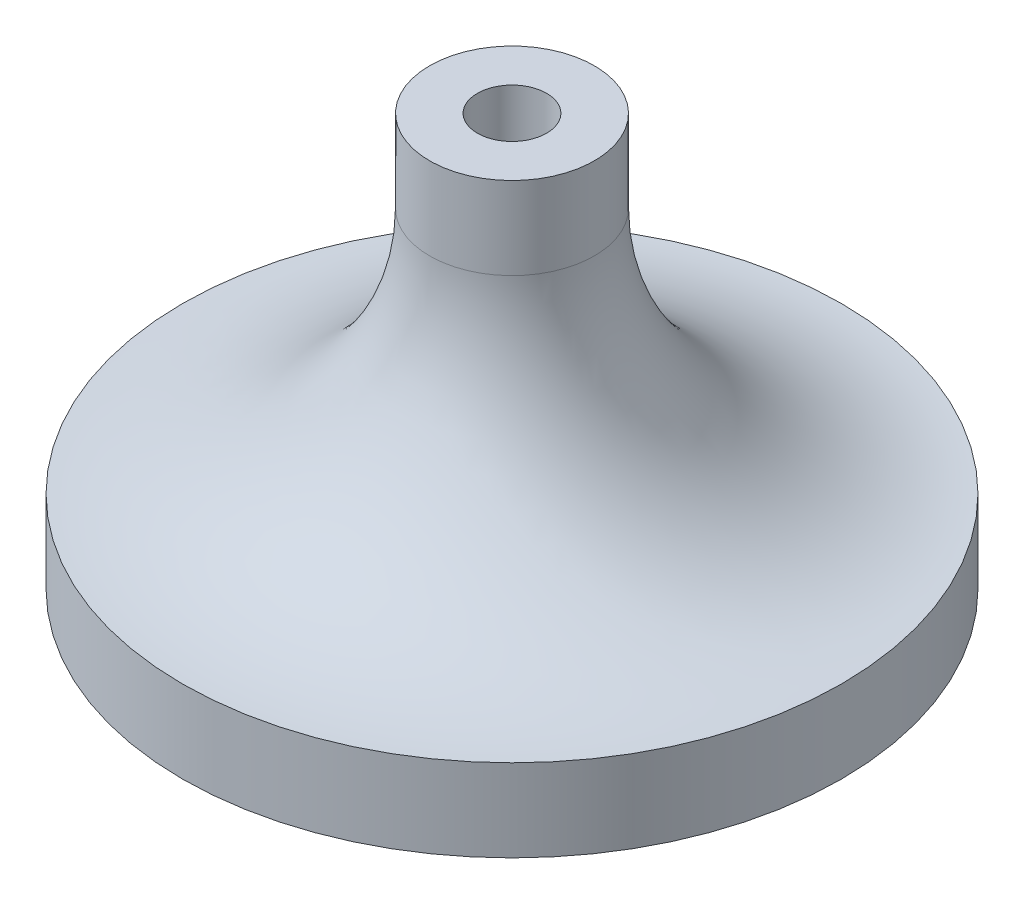
SolidWorks part; units mm, degrees
ref_plane "Front Plane" through (0, 0, 0) normal (0, 0, 1) x (1, 0, 0)
ref_plane "Top Plane" through (0, 0, 0) normal (0, 1, 0) x (1, 0, 0)
ref_plane "Right Plane" through (0, 0, 0) normal (1, 0, 0) x (0, 0, -1)
sketch "Sketch2" plane through (0, 0, 0) normal (0, 0, 1) x (1, 0, 0)
  line L0 (0, 0) -> (-20, 0)
  line L1 (-20, 0) -> (-20, 5)
  line L2 (-5, 20) -> (-5, 25)
  line L3 (-5, 25) -> (0, 25)
  line L4 (0, 25) -> (0, 0)
  arc A0 (-20, 5) -> (-5, 20) centre (-20, 20) ccw
  dimension "D1" = 20
  dimension "D2" = 5
  dimension "D3" = 5
  dimension "D4" = 25
revolve "Revolve1" add sketch "Sketch2" angle 360 about L4
hole_wizard "M5x0.8 Tapped Hole1" positions "Sketch3" profile "Sketch5" tap size "M5x0.8" standard "ANSI Metric"
sketch "Sketch3" plane through (0, 25, 0) normal (0, 1, 0) x (1, 0, 0)
  point P0 (0, 0)
sketch "Sketch5" plane through (0, 25, 0) normal (1, 0, 0) x (0, 0, 1)
  line L0 (0, 0) -> (0, 20.2618)
  line L1 (0, 20.2618) -> (2.1, 19)
  line L2 (2.1, 19) -> (2.1, 0)
  line L5 (2.1, 0) -> (0, 0)
  line L10 (0, 20.2618) -> (-2.1, 19) construction
  line L11 (0, -6.35) -> (0, 107.95) construction
  dimension "Tap Drill Dia." = 4.2
  dimension "Tap Drill Depth" = 19
  dimension "Drill Angle" = 118
cosmetic thread "Hole Thread1" parameters "D1"=10, "D2"=5
